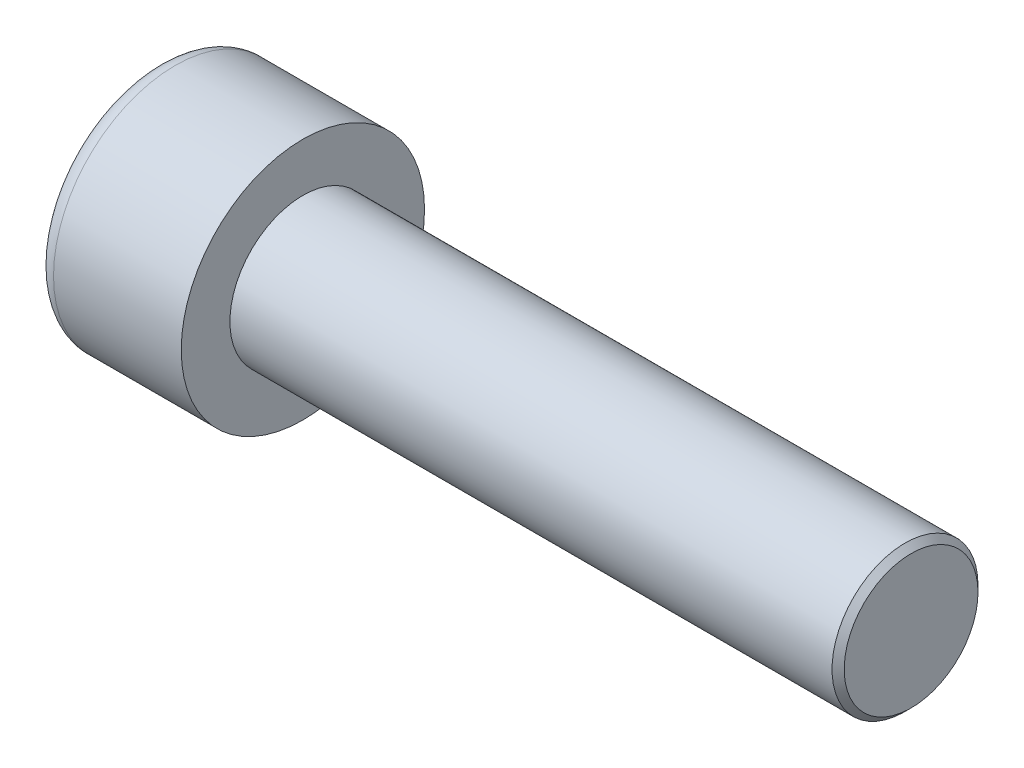
SolidWorks part; units mm, degrees
ref_plane "Front" through (0, 0, 0) normal (0, 0, 1) x (1, 0, 0)
ref_plane "Top" through (0, 0, 0) normal (0, 1, 0) x (1, 0, 0)
ref_plane "Right" through (0, 0, 0) normal (1, 0, 0) x (0, 0, -1)
sketch "Sketch1" plane through (0, 0, 0) normal (1, 0, 0) x (0, 0, -1)
  circle A0 centre (0, 0) radius 5
  dimension "dk" = 10
extrude "BaseHead" add sketch "Sketch1" along normal blind 6
sketch "Sketch2" plane through (6, 0, 0) normal (1, 0, 0) x (0, 0, -1)
  circle A0 centre (0, 0) radius 3
  dimension "d" = 6
extrude "BaseBody" add sketch "Sketch2" along normal blind 25
cosmetic thread "ThreadCosmetic1" parameters "b"=25, "D2"=4.917
sketch "Sketch3" plane through (0, 0, 0) normal (1, 0, 0) x (0, 0, -1)
  line L1 (2.8868, 0) -> (1.4434, 2.5)
  line L2 (1.4434, 2.5) -> (-1.4434, 2.5)
  line L3 (-1.4434, 2.5) -> (-2.8868, 0)
  line L4 (-2.8868, 0) -> (-1.4434, -2.5)
  line L5 (-1.4434, -2.5) -> (1.4434, -2.5)
  line L6 (1.4434, -2.5) -> (2.8868, 0)
  circle A0 centre (0, 0) radius 2.5 construction
  dimension "s" = 5
  dimension "e" = 5.7735
extrude "HexagonSocket" cut sketch "Sketch3" along normal blind 3
sketch "Sketch4" plane through (-4.1961, 0.75, 0) normal (0, 0, 1) x (-1, 0, 0)
  line L0 (-7.1961, 3.25) -> (-8.6395, 0.75)
  line L2 (-8.6395, 0.75) -> (-7.1961, 0.75)
  line L3 (-7.1961, 0.75) -> (-7.1961, 3.25)
  line L4 (-5.0351, 0.75) -> (0.839, 0.75) construction
  line L5 (-35.1961, 0.75) -> (-10.1961, 0.75) construction
  line L6 (-10.1961, 0.75) -> (-4.1961, 0.75) construction
  dimension "m" = 60
revolve "Cut-Revolve1" cut sketch "Sketch4" angle 360 about L4
fillet "HeadFillet" [suppressed] radius 0.25
fillet "TopFillet" radius 0.75 1 edges at (0, 0, -5)
chamfer "Chamfer1" distance 0.25 angle 45 1 edges at (31, 0, -3)
sketch "Sketch5" plane through (0, 0, 0) normal (0, 0, 1) x (1, 0, 0)
  line L0 (30.75, 2.531) -> (31.0207, 3)
  line L1 (31.0207, 3) -> (31.0207, 3.5415)
  line L2 (31.0207, 3.5415) -> (30.4792, 3.5415)
  line L3 (30.4792, 3.5415) -> (30.4792, 3)
  line L4 (30.4792, 3) -> (30.75, 2.531)
  line L5 (0, 0) -> (7.8886, 0) construction
  line L6 (30.75, -3) -> (30.75, 3) construction
  dimension "D1" = 6
  dimension "D2" = 0.5415
revolve "Cut-Revolve10" [suppressed] cut sketch "Sketch5" angle 360 about L5
pattern_linear "LPattern10" [suppressed] count 38 spacing 0.6498 along (1, 0, 0)
equation "\"r1@TopFillet\" = \"d@Sketch2\" / 8"
equation "\"D1@Chamfer1\" = \"r@HeadFillet\""
equation "\"D1@Sketch5\" = \"d@Sketch2\""
equation "\"D2@Sketch5\" =  ( \"d@Sketch2\" - \"D2@ThreadCosmetic1\" )  / 2"
equation "\"D3@LPattern10\" = \"D2@Sketch5\" * 1.2"
equation "\"D1@LPattern10\" = \"b@ThreadCosmetic1\" / \"D3@LPattern10\""
